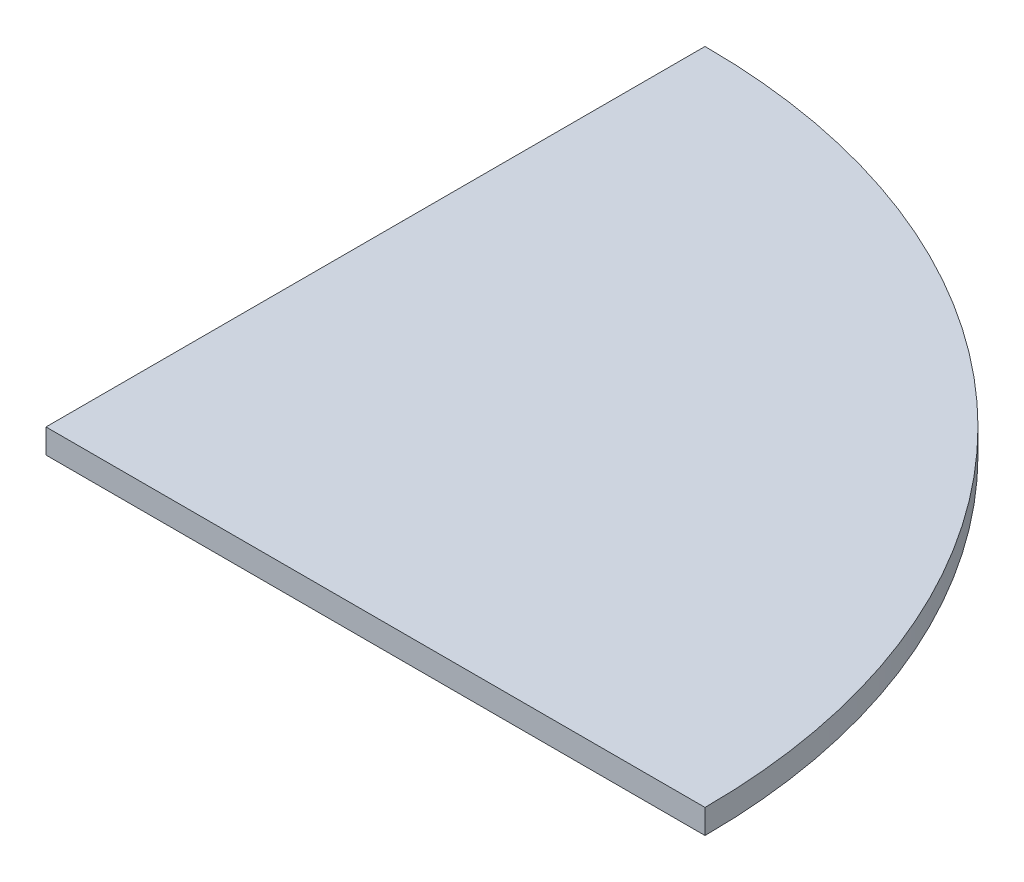
SolidWorks part; units mm, degrees
ref_plane "Front Plane" through (0, 0, 0) normal (0, 0, 1) x (1, 0, 0)
ref_plane "Top Plane" through (0, 0, 0) normal (0, 1, 0) x (1, 0, 0)
ref_plane "Right Plane" through (0, 0, 0) normal (1, 0, 0) x (0, 0, -1)
sketch "Sketch1" plane through (0, 0, 0) normal (0, 1, 0) x (1, 0, 0)
  line L0 (0, 618.236) -> (0, 0)
  line L1 (0, 0) -> (618.236, 0)
  arc A0 (618.236, 0) -> (0, 618.236) centre (0, 0) ccw
  dimension "D1" = 1236.472
extrude "Boss-Extrude1" add sketch "Sketch1" along normal mid plane 22.86
